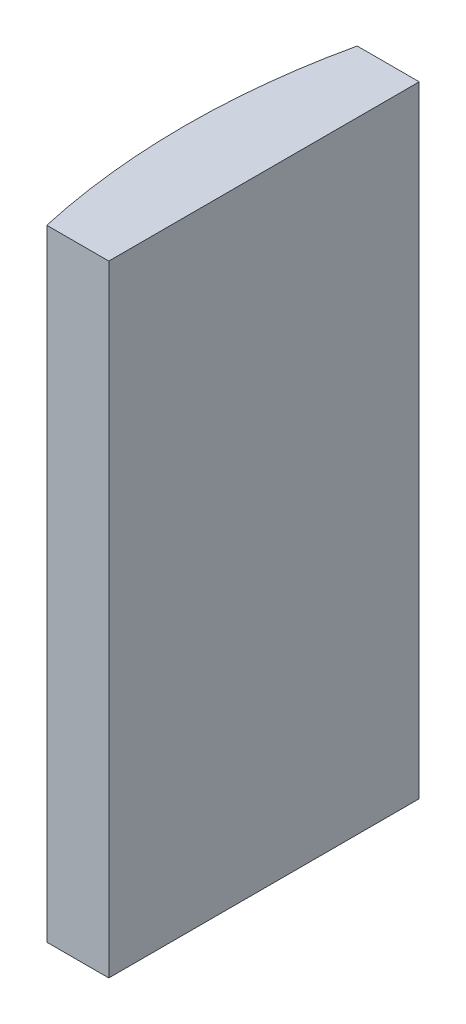
SolidWorks part; units mm, degrees
ref_plane "前视基准面" through (0, 0, 0) normal (0, 0, 1) x (1, 0, 0)
ref_plane "上视基准面" through (0, 0, 0) normal (0, 1, 0) x (1, 0, 0)
ref_plane "右视基准面" through (0, 0, 0) normal (1, 0, 0) x (0, 0, -1)
sketch "草图1" plane through (0, 0, 0) normal (0, 1, 0) x (1, 0, 0)
  line L0 (-137.6835, 0) -> (10.8051, 0) construction
  line L1 (-18.0128, 5) -> (-16.0148, 5)
  line L2 (-18.0128, -5) -> (-16.0148, -5)
  line L3 (-16.0148, 5) -> (-16.0148, -5)
  arc A0 (-18.0128, 5) -> (-18.0128, -5) centre (4.3552, 0) ccw
  point P2 (-18.5648, 0)
  point P4 (-16.0148, 0)
  dimension "D2" = 5
  dimension "D3" = 22.92
  dimension "D4" = 2.55
  dimension "D1" = 5
extrude "凸台-拉伸1" add sketch "草图1" along normal blind 20
